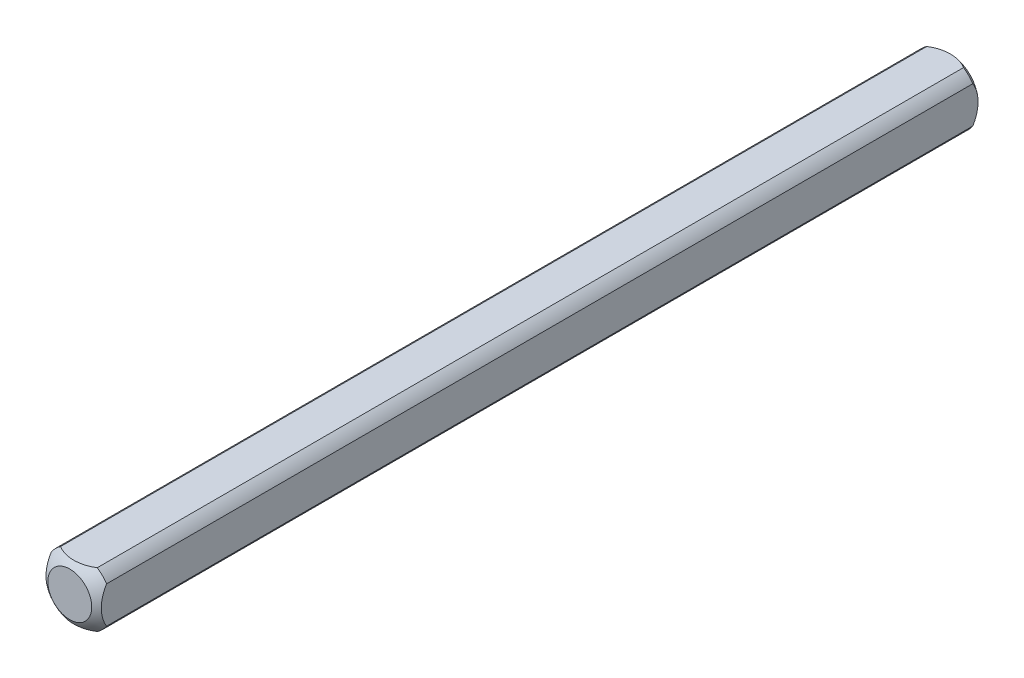
SolidWorks part; units mm, degrees
material "Custom Plastic"
ref_plane "Front Plane" through (0, 0, 0) normal (0, 0, 1) x (1, 0, 0)
ref_plane "Top Plane" through (0, 0, 0) normal (0, 1, 0) x (1, 0, 0)
ref_plane "Right Plane" through (0, 0, 0) normal (1, 0, 0) x (0, 0, -1)
sketch "Sketch1" plane through (0, 0, 0) normal (0, 0, 1) x (1, 0, 0)
  line L0 (-3.175, -3.175) -> (3.175, 3.175) construction
  line L1 (-3.175, -3.175) -> (3.175, -3.175)
  line L2 (-3.175, -3.175) -> (-3.175, 3.175)
  line L3 (-3.175, 3.175) -> (3.175, 3.175)
  line L4 (3.175, -3.175) -> (3.175, 3.175)
  dimension "D1" = 6.35
extrude "Boss-Extrude1" add sketch "Sketch1" along normal blind 50.8
sketch "Sketch2" plane through (0, 0, 0) normal (0, 0, -1) x (-1, 0, 0)
  circle A0 centre (0, 0) radius 3.81
  dimension "D1" = 7.62
extrude "Cut-Extrude1" cut sketch "Sketch2" against normal through all flip side to cut
ref_axis "Axis1" through (0, 0, 50.8) along (0, 0, -1)
sketch "Sketch3" plane through (0, 0, 0) normal (0, 1, 0) x (1, 0, 0)
  line L1 (-5.0537, -3.8933) -> (-5.0537, 5.7405)
  line L2 (-5.0537, 5.7405) -> (0, 5.7405)
  line L5 (0, -50.8) -> (0, 0) construction
  line L8 (0, 0.6703) -> (0, 5.7405)
  arc A0 (-5.0537, -3.8933) -> (0, 0.6703) centre (0, -4.4097) cw
  dimension "D1" = 5.08
revolve "Cut-Revolve1" cut sketch "Sketch3" angle 360 about axis through (0, 0, 50.8) along (0, 0, -1)
mirror "Mirror1" about plane through (0, 0, 50.8) normal (0, 0, -1) of bodies 103
